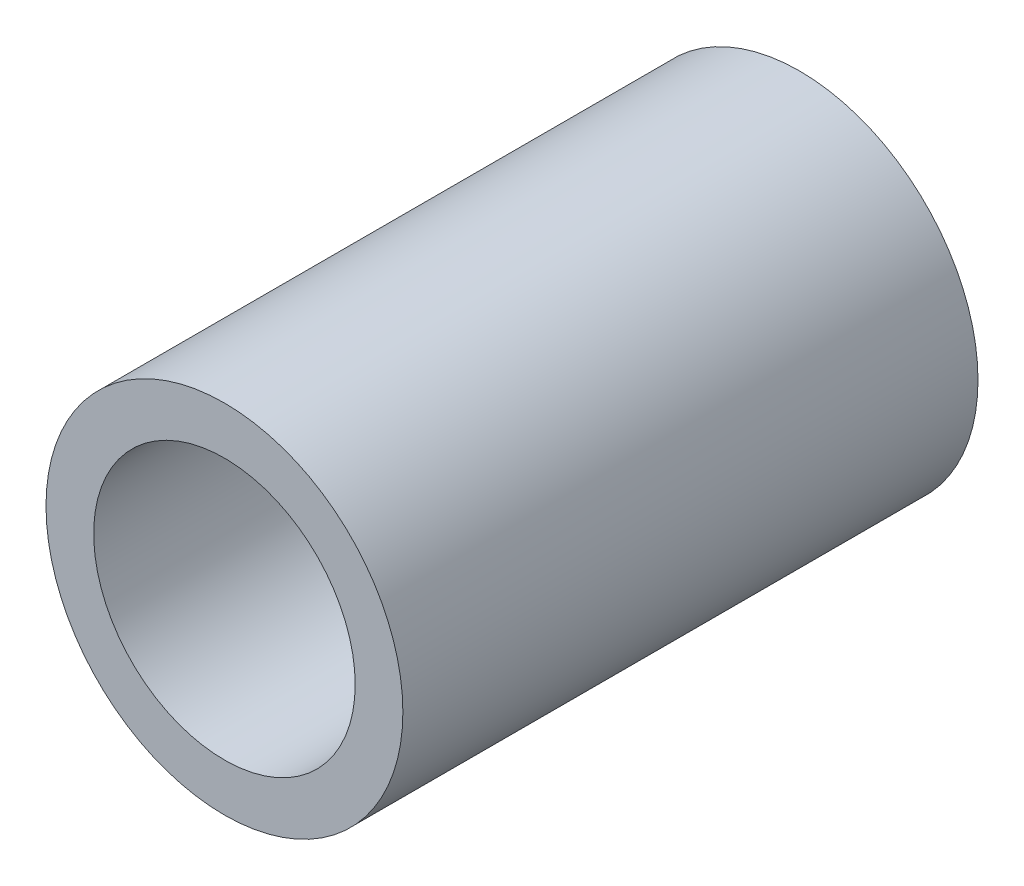
SolidWorks part; units mm, degrees
material "PVC 0.007 Plasticized"
ref_plane "Front Plane" through (0, 0, 0) normal (0, 0, 1) x (1, 0, 0)
ref_plane "Top Plane" through (0, 0, 0) normal (0, 1, 0) x (1, 0, 0)
ref_plane "Right Plane" through (0, 0, 0) normal (1, 0, 0) x (0, 0, -1)
sketch "Sketch1" plane through (0, 0, 0) normal (0, 0, 1) x (1, 0, 0)
  circle A1 centre (0, 0) radius 4.6101
  dimension "D1" = 9.2202
extrude "Boss-Extrude1" add sketch "Sketch1" against normal blind 14.859
hole_wizard "H (0.266) Diameter Hole1" positions "Sketch2" profile "Sketch3" hole size "H" standard "ANSI Inch" end condition through all
sketch "Sketch2" plane through (0, 0, 0) normal (0, 0, 1) x (1, 0, 0)
  point P0 (0, 0)
sketch "Sketch3" plane through (0, 0, 0) normal (1, 0, 0) x (0, -1, 0)
  line L0 (0, 0) -> (0, 14.859)
  line L1 (0, 14.859) -> (3.3782, 14.859)
  line L2 (3.3782, 14.859) -> (3.3782, 0)
  line L5 (3.3782, 0) -> (0, 0)
  line L11 (0, -6.35) -> (0, 107.95) construction
  dimension "Thru Hole Dia." = 6.7564
  dimension "Thru Hole Depth" = 14.859
